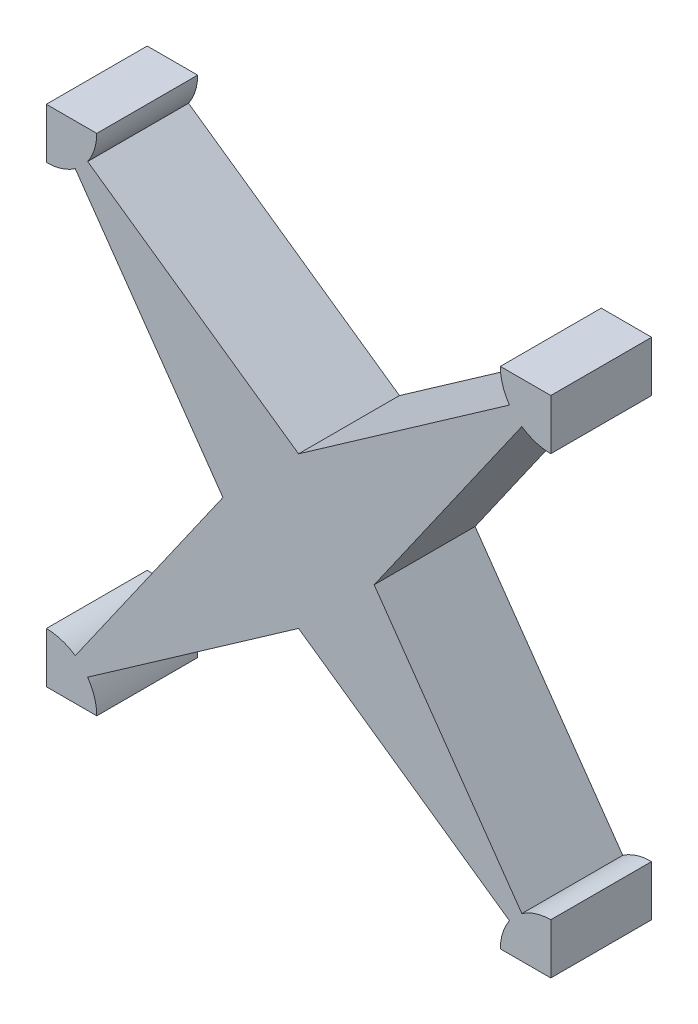
SolidWorks part; units mm, degrees
material "Rubber"
ref_plane "Front Plane" through (0, 0, 0) normal (0, 0, 1) x (1, 0, 0)
ref_plane "Top Plane" through (0, 0, 0) normal (0, 1, 0) x (1, 0, 0)
ref_plane "Right Plane" through (0, 0, 0) normal (1, 0, 0) x (0, 0, -1)
sketch "Sketch1" plane through (0, 0, 0) normal (0, 0, 1) x (1, 0, 0)
  line L0 (0, 12.5) -> (25, 12.5) construction
  line L1 (0, 0) -> (25, 0) construction
  line L2 (0, 0) -> (0, 25) construction
  line L3 (0, 25) -> (25, 25) construction
  line L4 (25, 0) -> (25, 25) construction
  line L5 (12.5, 25) -> (12.5, 0) construction
  line L6 (0, 0) -> (25, 25) construction
  line L7 (0, 25) -> (25, 0) construction
  line L16 (0, 0) -> (8.7526, 12.5)
  line L17 (0, 0) -> (12.5, 8.7526)
  line L18 (12.5, 8.7526) -> (25, 0)
  line L19 (25, 0) -> (16.2474, 12.5)
  line L20 (16.2474, 12.5) -> (25, 25)
  line L21 (25, 25) -> (12.5, 16.2474)
  line L22 (12.5, 16.2474) -> (0, 25)
  line L23 (0, 25) -> (8.7526, 12.5)
  dimension "D1" = 25
  dimension "D2" = 35
  dimension "D3" = 25
  dimension "D4" = 35
  dimension "D5" = 35
  dimension "D6" = 35
extrude "Boss-Extrude1" add sketch "Sketch1" along normal blind 5
sketch "Sketch2" plane through (0, 0, 5) normal (0, 0, 1) x (1, 0, 0)
  line L0 (0, 0) -> (25, 0) construction
  line L1 (25, 0) -> (25, 25) construction
  line L2 (0, 25) -> (25, 25) construction
  line L3 (0, 0) -> (0, 25) construction
  line L4 (0, 0) -> (25, 0) construction
  line L5 (25, 0) -> (25, 25) construction
  line L6 (0, 25) -> (25, 25) construction
  line L7 (0, 0) -> (0, 25) construction
  line L8 (0, 22.5) -> (0, 25)
  line L9 (0, 25) -> (2.5, 25)
  line L10 (12.5, 25) -> (12.5, 0) construction
  line L11 (12.5, 25) -> (12.5, 0) construction
  line L12 (0, 12.5) -> (25, 12.5) construction
  line L13 (0, 12.5) -> (25, 12.5) construction
  line L14 (25, 22.5) -> (25, 25)
  line L15 (25, 25) -> (22.5, 25)
  line L16 (25, 0) -> (22.5, 0)
  line L17 (25, 2.5) -> (25, 0)
  line L18 (0, 2.5) -> (0, 0)
  line L19 (0, 0) -> (2.5, 0)
  arc A0 (2.5, 25) -> (0, 22.5) centre (0, 25) cw
  arc A1 (22.5, 25) -> (25, 22.5) centre (25, 25) ccw
  arc A2 (22.5, 0) -> (25, 2.5) centre (25, 0) cw
  arc A3 (2.5, 0) -> (0, 2.5) centre (0, 0) ccw
  dimension "D1" = 2.5
extrude "Boss-Extrude2" add sketch "Sketch2" against normal up to surface (5 mm away) up to face at (12.5, 12.5, 0)
equation "\"d\"=30"
